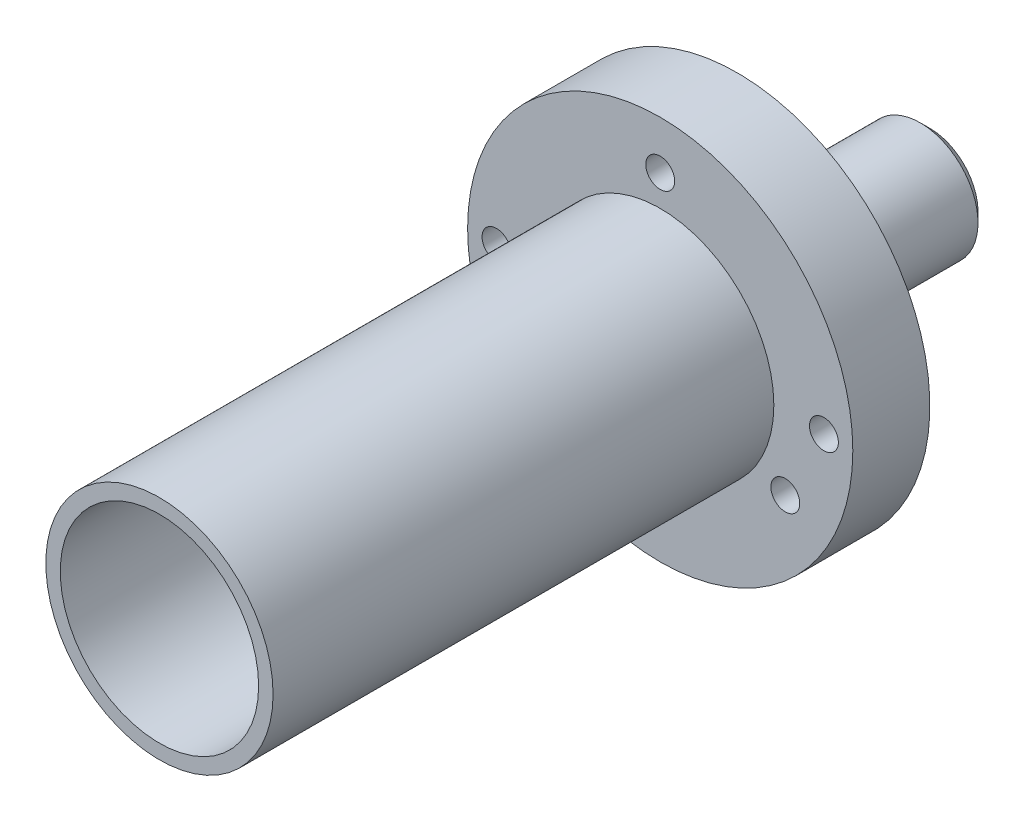
SolidWorks part; units mm, degrees
ref_plane "Front Plane" through (0, 0, 0) normal (0, 0, 1) x (1, 0, 0)
ref_plane "Top Plane" through (0, 0, 0) normal (0, 1, 0) x (1, 0, 0)
ref_plane "Right Plane" through (0, 0, 0) normal (1, 0, 0) x (0, 0, -1)
sketch "Sketch1" plane through (0, 0, 0) normal (0, 0, 1) x (1, 0, 0)
  circle A0 centre (0, 0) radius 5.15
  circle A1 centre (0, 0) radius 10
  dimension "D1" = 10.3
  dimension "D2" = 20
extrude "Boss-Extrude1" add sketch "Sketch1" along normal blind 2
sketch "Sketch3" plane through (0, 0, 0) normal (0, 0, -1) x (-1, 0, 0)
  circle A0 centre (0, 0) radius 3
  dimension "D1" = 6
extrude "Boss-Extrude2" add sketch "Sketch3" along normal blind 12 separate body
sketch "Sketch4" plane through (0, 0, 0) normal (0, 0, -1) x (-1, 0, 0)
  circle A0 centre (0, 0) radius 10 construction
  circle A2 centre (0, 0) radius 10
  circle A4 centre (0, 0) radius 3 construction
  circle A5 centre (0, 0) radius 3
extrude "Boss-Extrude3" add sketch "Sketch4" along normal blind 2
chamfer "Chamfer2" distance 1 angle 45 1 edges at (-3, 0, -2)
chamfer "Chamfer4" distance 0.5 angle 45 1 edges at (-3, 0, -12)
sketch "Sketch5" plane through (0, 0, -2) normal (0, 0, -1) x (-1, 0, 0)
  line L0 (-10, 0) -> (10, 0) construction
  circle A0 centre (0, 0) radius 10 construction
  circle A1 centre (-8.5, 0) radius 0.75
  circle A2 centre (8.5, 0) radius 0.75
  circle A3 centre (0, 0) radius 4 construction
  point P9 (4, 0)
  dimension "D1" = 1.5
  dimension "D2" = 1.5
  dimension "D3" = 1.5
  dimension "D4" = 1.5
extrude "Cut-Extrude1" cut sketch "Sketch5" against normal up to next
sketch "Sketch6" plane through (0, 0, 2) normal (0, 0, 1) x (1, 0, 0)
  circle A0 centre (0, 0) radius 5.9
  circle A1 centre (0, 0) radius 5.15 construction
  circle A2 centre (0, 0) radius 5.15
  point P2 (0, 0)
  point P3 (1.3531, -0.9423)
  point P4 (0, 0)
  dimension "D1" = 0.75
extrude "Boss-Extrude4" add sketch "Sketch6" along normal blind 26
sketch "Sketch7" plane through (0, 0, -2) normal (0, 0, -1) x (-1, 0, 0)
  circle A0 centre (0, 0) radius 7.5 construction
  circle A1 centre (0, 7.5) radius 0.75
  circle A2 centre (6.4952, -3.75) radius 0.75
  circle A3 centre (-6.4952, -3.75) radius 0.75
  point P5 (0.3441, 6.9915)
  point P6 (0, 0)
  point P7 (0, 0)
  point P14 (0, 0)
  dimension "D1" = 15
  dimension "D2" = 1.5
  dimension "D3" = 3
extrude "Cut-Extrude2" cut sketch "Sketch7" against normal up to next
